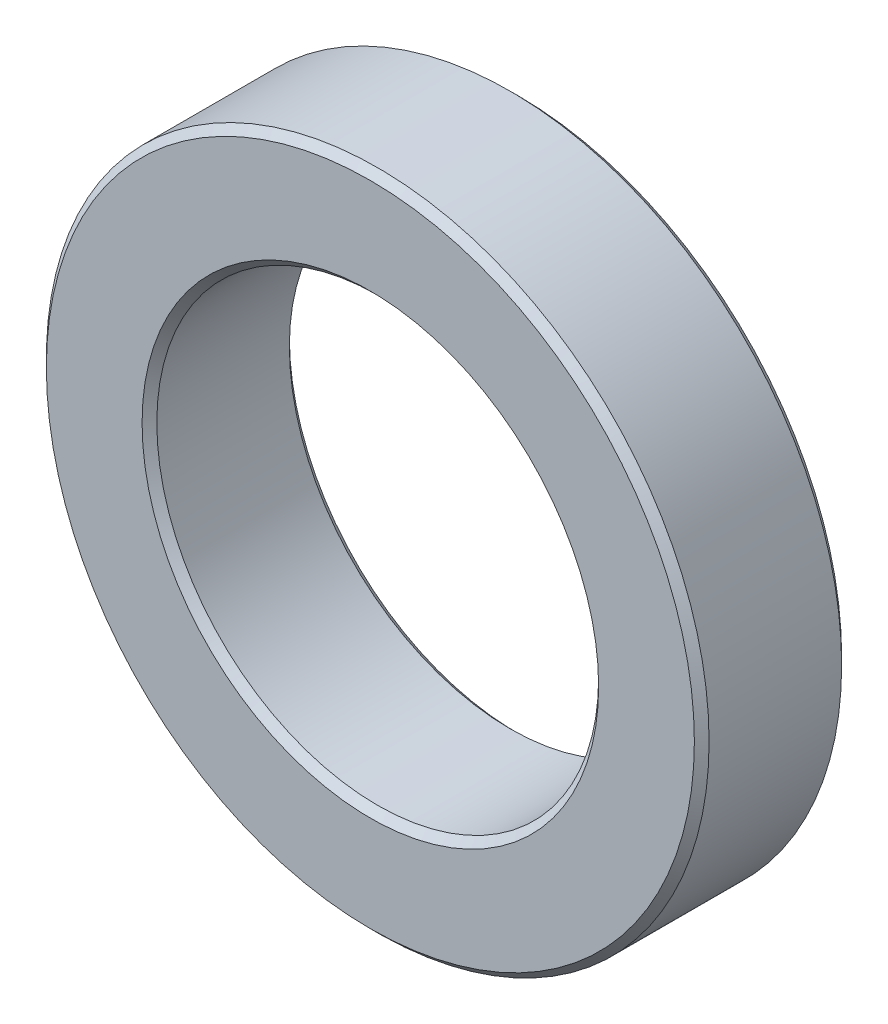
SolidWorks part; units mm, degrees
ref_plane "前视基准面" through (0, 0, 0) normal (0, 0, 1) x (1, 0, 0)
ref_plane "上视基准面" through (0, 0, 0) normal (0, 1, 0) x (1, 0, 0)
ref_plane "右视基准面" through (0, 0, 0) normal (1, 0, 0) x (0, 0, -1)
sketch "草图1" plane through (0, 0, 0) normal (0, 0, 1) x (1, 0, 0)
  circle A0 centre (0, 0) radius 1.5
  circle A1 centre (0, 0) radius 2.25
  dimension "D1" = 3
  dimension "D2" = 4.5
extrude "凸台-拉伸1" add sketch "草图1" along normal blind 1
chamfer "倒角1" distance 0.05 angle 45 4 edges at (1.5, 0, 1) (1.5, 0, 0) (2.25, 0, 0) (2.25, 0, 1)
